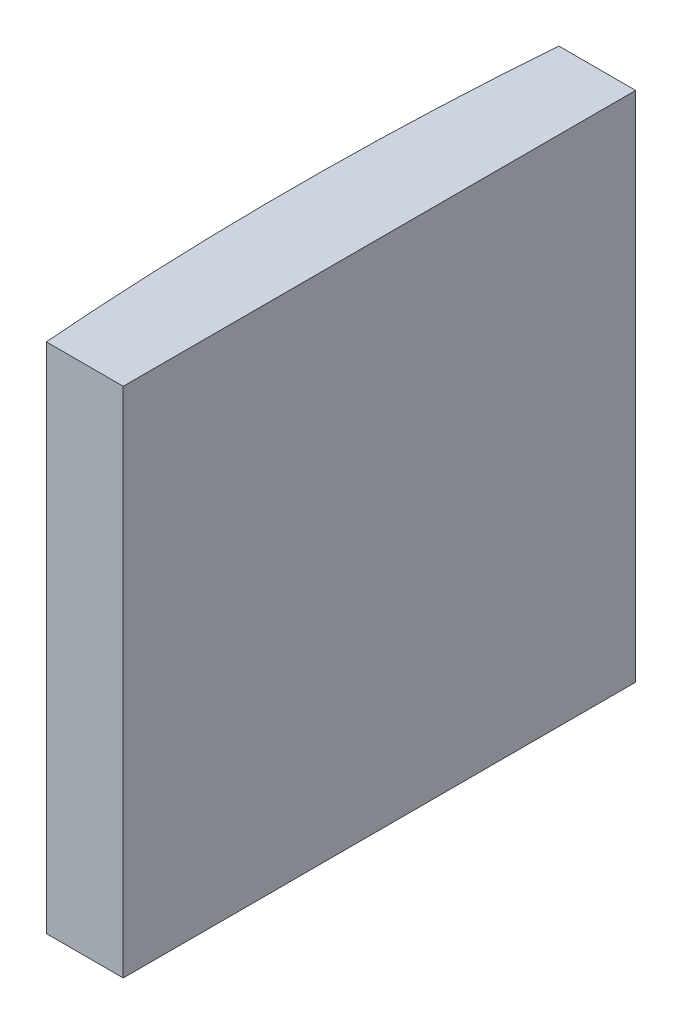
SolidWorks part; units mm, degrees
ref_plane "前视基准面" through (0, 0, 0) normal (0, 0, 1) x (1, 0, 0)
ref_plane "上视基准面" through (0, 0, 0) normal (0, 1, 0) x (1, 0, 0)
ref_plane "右视基准面" through (0, 0, 0) normal (1, 0, 0) x (0, 0, -1)
sketch "草图1" plane through (0, 0, 0) normal (0, 1, 0) x (1, 0, 0)
  line L0 (10.7432, 0) -> (-141.213, 0) construction
  line L1 (-124.5074, 10) -> (-121.5048, 10)
  line L2 (-124.5074, -10) -> (-121.5048, -10)
  line L3 (-121.5048, 10) -> (-121.5048, -10)
  arc A0 (-124.5074, 10) -> (-124.5074, -10) centre (4.3552, 0) ccw
  point P2 (-141.213, 0)
  point P19 (-124.8948, 0)
  point P20 (-121.5048, 0)
  dimension "D2" = 10
  dimension "D3" = 129.25
  dimension "D4" = 3.39
  dimension "D1" = 10
extrude "凸台-拉伸1" add sketch "草图1" along normal blind 20
